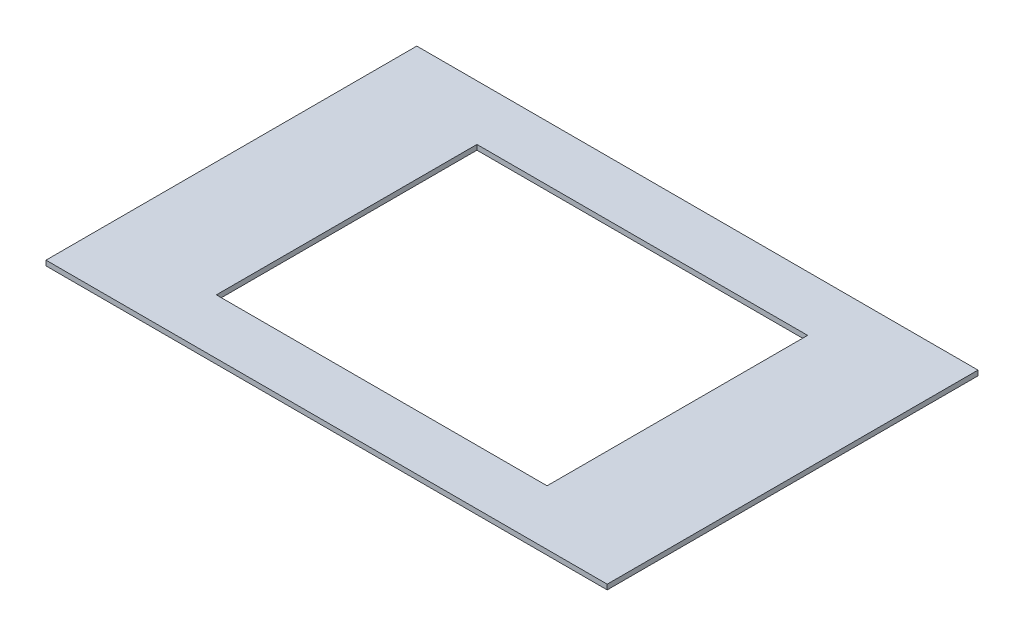
SolidWorks part; units mm, degrees
ref_plane "Front Plane" through (0, 0, 0) normal (0, 0, 1) x (1, 0, 0)
ref_plane "Top Plane" through (0, 0, 0) normal (0, 1, 0) x (1, 0, 0)
ref_plane "Right Plane" through (0, 0, 0) normal (1, 0, 0) x (0, 0, -1)
sketch "Sketch1" plane through (0, 0, 0) normal (0, 1, 0) x (1, 0, 0)
  line L1 (-56, 37) -> (56, 37)
  line L2 (-56, 37) -> (-56, -37)
  line L3 (-56, -37) -> (56, -37)
  line L4 (56, 37) -> (56, -37)
  line L5 (-56, 37) -> (56, -37) construction
  line L6 (-56, -37) -> (56, 37) construction
  point P0 (0, 0)
  dimension "D1" = 112
  dimension "D2" = 74
extrude "Boss-Extrude1" add sketch "Sketch1" along normal blind 1
sketch "Sketch5" plane through (0, 1, 0) normal (0, 1, 0) x (1, 0, 0)
  line L1 (-33, 26) -> (33, 26)
  line L2 (-33, 26) -> (-33, -26)
  line L3 (-33, -26) -> (33, -26)
  line L4 (33, 26) -> (33, -26)
  line L5 (-33, 26) -> (33, -26) construction
  line L6 (-33, -26) -> (33, 26) construction
  point P0 (0, 0)
  dimension "D1" = 66
  dimension "D2" = 52
extrude "Cut-Extrude2" cut sketch "Sketch5" against normal blind 2
